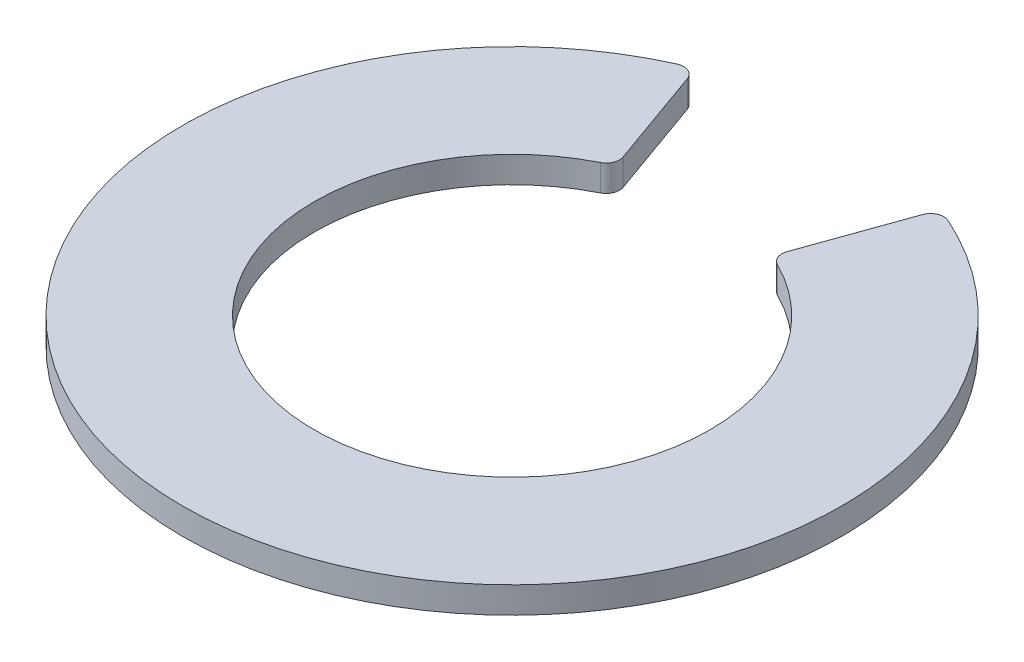
SolidWorks part; units mm, degrees
ref_plane "Front Plane" through (0, 0, 0) normal (0, 0, 1) x (1, 0, 0)
ref_plane "Top Plane" through (0, 0, 0) normal (0, 1, 0) x (1, 0, 0)
ref_plane "Right Plane" through (0, 0, 0) normal (1, 0, 0) x (0, 0, -1)
sketch "Sketch4" plane through (0, 0, 0) normal (0, 1, 0) x (1, 0, 0)
  line L0 (-0.8923, 2.2215) -> (-0.622, 1.4644)
  line L1 (0.8923, 2.2215) -> (0.622, 1.4644)
  arc A0 (-0.6715, 1.3413) -> (0.6715, 1.3413) centre (0, 0) ccw
  arc A1 (-1.0276, 2.2791) -> (1.0276, 2.2791) centre (0, 0) ccw
  arc A2 (0.6715, 1.3413) -> (0.622, 1.4644) centre (0.7162, 1.4307) cw
  arc A3 (1.0276, 2.2791) -> (0.8923, 2.2215) centre (0.9865, 2.1879) ccw
  arc A4 (-0.6715, 1.3413) -> (-0.622, 1.4644) centre (-0.7162, 1.4307) ccw
  arc A5 (-1.0276, 2.2791) -> (-0.8923, 2.2215) centre (-0.9865, 2.1879) cw
  point P8 (0.5914, 1.3785)
  point P11 (0.928, 2.3214)
  point P14 (-0.5914, 1.3785)
  point P17 (-0.928, 2.3214)
  dimension "D1" = 1.5
  dimension "D2" = 2.5
  dimension "D3" = 0.1
extrude "Boss-Extrude1" add sketch "Sketch4" along normal blind 0.2
